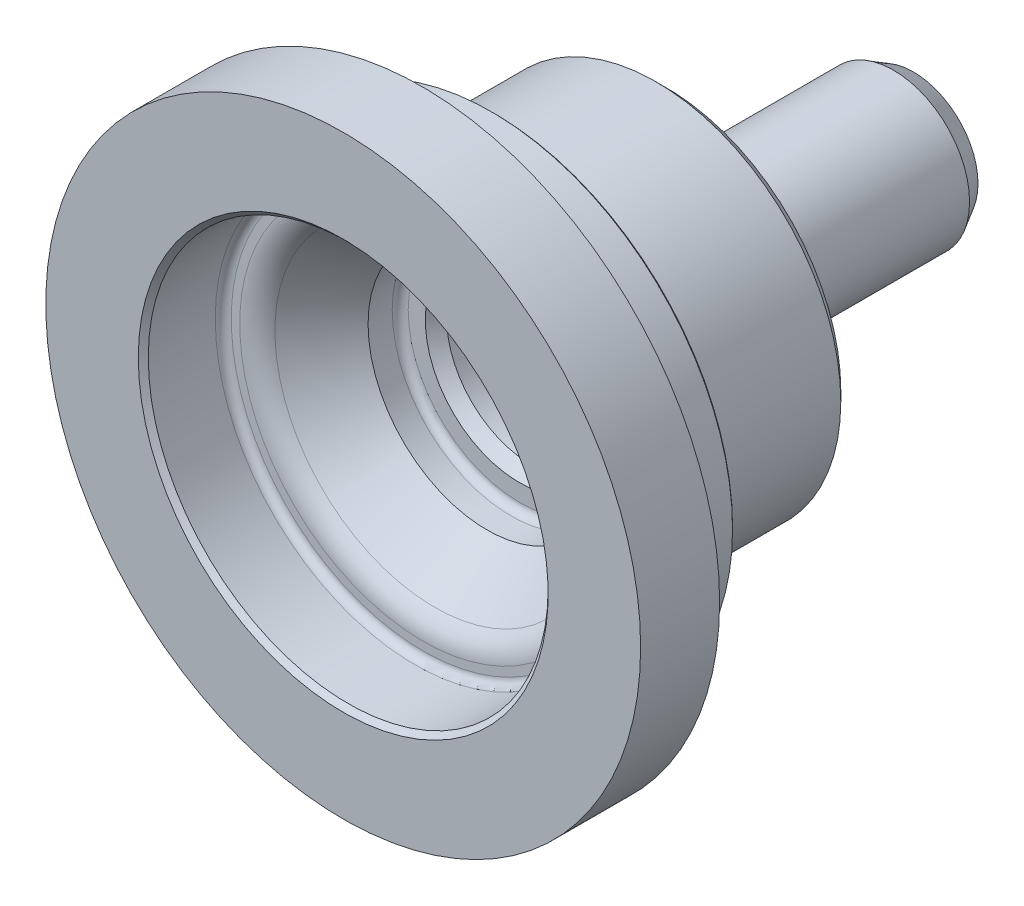
SolidWorks part; units mm, degrees
ref_plane "Ebene vorne" through (0, 0, 0) normal (0, 0, 1) x (1, 0, 0)
ref_plane "Ebene oben" through (0, 0, 0) normal (0, 1, 0) x (1, 0, 0)
ref_plane "Ebene rechts" through (0, 0, 0) normal (1, 0, 0) x (0, 0, -1)
sketch "Skizze1" plane through (0, 0, 0) normal (1, 0, 0) x (0, 0, -1)
  line L0 (0, 0) -> (57.5, 0) construction
  line L1 (57.5, 0) -> (57.5, 5.8)
  line L2 (17.6, 9.3875) -> (17.6, 11.1)
  line L3 (32.3, 10.25) -> (32.3, 18.47)
  line L4 (32.3, 18.47) -> (18.85, 18.47)
  line L5 (15.05, 18.47) -> (15.05, 24.1125)
  line L6 (15.05, 24.1125) -> (7.9, 24.1125)
  line L7 (7.9, 27.2115) -> (7.9, 29.75)
  line L8 (7.9, 29.75) -> (0, 29.75)
  line L9 (0, 29.75) -> (0, 20)
  line L10 (0, 20) -> (7.2, 20)
  line L11 (31.3, 0) -> (31.3, 5.5)
  line L12 (27.3, 5.5) -> (27.3, 7.65)
  line L13 (26.5, 8.45) -> (18.8, 8.45)
  line L14 (31.3, 5.5) -> (27.3, 5.5)
  line L15 (18.8, 8.45) -> (17.6, 9.3875)
  line L16 (18.8, 8.45) -> (8, 8.45) construction
  line L17 (8, 19.2) -> (8, 18.3511)
  line L18 (31.3, 0) -> (57.5, 0)
  line L19 (18.85, 18.47) -> (17.0833, 17.45)
  line L20 (16.07, 17.45) -> (17.0833, 17.45)
  line L21 (55.05, 7.6) -> (57.0469, 6.4471)
  line L22 (7.9, 24.1125) -> (7.15, 24.1125)
  line L23 (7.9, 27.2115) -> (6.6304, 25.0125)
  line L24 (16.8, 11.9) -> (14.3842, 11.9)
  line L25 (55.05, 7.6) -> (36.7062, 7.6)
  line L26 (57.0469, 6.4471) -> (57.5, 5.8)
  line L27 (14.3842, 11.9) -> (9.153, 15.9871)
  arc A0 (15.05, 18.47) -> (16.07, 17.45) centre (16.07, 18.47) ccw
  arc A1 (6.6304, 25.0125) -> (7.15, 24.1125) centre (7.15, 24.7125) ccw
  arc A2 (32.3, 10.25) -> (36.7062, 7.6) centre (35.3, 10.25) ccw
  arc A3 (8, 18.3511) -> (9.153, 15.9871) centre (11, 18.3511) ccw
  arc A4 (17.6, 11.1) -> (16.8, 11.9) centre (16.8, 11.1) ccw
  arc A5 (27.3, 7.65) -> (26.5, 8.45) centre (26.5, 7.65) ccw
  arc A6 (8, 19.2) -> (7.2, 20) centre (7.2, 19.2) ccw
  point P5 (17.6, 0)
  point P13 (51, 0)
  point P17 (18.85, 18.47)
  point P50 (57.5, 5)
  dimension "D16" = 7.15
  dimension "D14" = 17.6
  dimension "D20" = 1.6
  dimension "D1" = 57.5
  dimension "D3" = 18.47
  dimension "D4" = 24.1125
  dimension "D5" = 29.75
  dimension "D6" = 20
  dimension "D7" = 6.5
  dimension "D8" = 31.3
  dimension "D9" = 27.3
  dimension "D10" = 38
  dimension "D11" = 18.85
  dimension "D12" = 30
  dimension "D13" = 17.45
  dimension "D15" = 30
  dimension "D17" = 7.9
  dimension "D18" = 15.05
  dimension "D19" = 22.75
  dimension "D21" = 5.8
  dimension "D24" = 5
revolve "Rotation1" add sketch "Skizze1" angle 360 about L0
chamfer "Fase1" distance 1 angle 45 1 edges at (18.47, 0, -32.3)
chamfer "Fase2" distance 0.22 angle 45 1 edges at (24.1125, 0, -15.05)
chamfer "Fase3" distance 0.5 angle 45 1 edges at (20, 0, 0)
sketch "Skizze14" plane through (0, 0, -57.5) normal (0, 0, -1) x (-1, 0, 0)
  point P0 (0, 0)
hole_wizard "Formsenkung für M3 Linsensenkschraube mit Schlitz3" positions "Skizze18" profile "Skizze17" countersink size "M3" standard "DIN"
sketch "Skizze18" plane through (0, 0, -57.5) normal (0, 0, -1) x (-1, 0, 0)
  point P0 (0, 0)
sketch "Skizze17" plane through (0, 0, -57.5) normal (1, 0, 0) x (0, 1, 0)
  line L0 (0, 0) -> (0, 7.5215)
  line L1 (0, 7.5215) -> (1.7, 6.5)
  line L2 (1.7, 6.5) -> (1.7, 1.65)
  line L3 (1.7, 1.65) -> (3.35, 0)
  line L5 (3.35, 0) -> (0, 0)
  line L6 (-1.7, 1.65) -> (-3.35, 0) construction
  line L10 (0, 7.5215) -> (-1.7, 6.5) construction
  line L11 (0, -6.35) -> (0, 107.95) construction
  dimension "Bohrerdurchmesser" = 3.4
  dimension "Bohrungstiefe" = 6.5
  dimension "Senkdurchmesser (Oben)" = 6.7
  dimension "Senkwinkel (Oben)" = 90
  dimension "Spitzenwinkel" = 118
